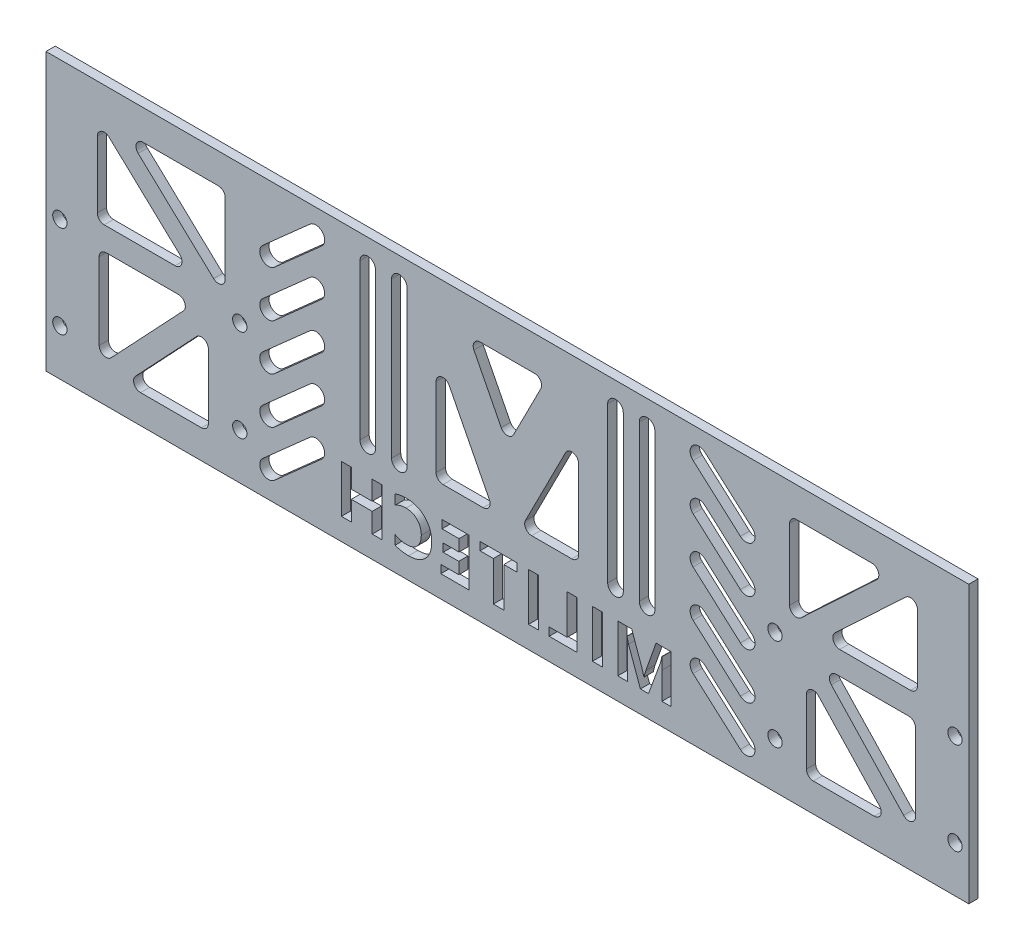
SolidWorks part; units mm, degrees
material "Thornel Mat VMA"
ref_plane "前视基准面" through (0, 0, 0) normal (0, 0, 1) x (1, 0, 0)
ref_plane "上视基准面" through (0, 0, 0) normal (0, 1, 0) x (1, 0, 0)
ref_plane "右视基准面" through (0, 0, 0) normal (1, 0, 0) x (0, 0, -1)
sketch "草图1" plane through (0, 0, 0) normal (0, 0, 1) x (1, 0, 0)
  line L1 (69.1181, 5.8229) -> (69.1181, -30.1771)
  line L2 (69.1181, -30.1771) -> (22.1181, -30.1771)
  line L6 (-83.8819, -30.1771) -> (-130.8819, -30.1771)
  line L7 (-130.8819, -30.1771) -> (-130.8819, 5.8229)
  line L9 (-83.8819, -30.1771) -> (22.1181, -30.1771)
  line L10 (-130.8819, 29.8229) -> (69.1181, 29.8229)
  line L11 (69.1181, 29.8229) -> (69.1181, 5.8229)
  line L12 (-130.8819, 5.8229) -> (-130.8819, 29.8229)
  line L13 (-30.8819, 70.3505) -> (-30.8819, -56.6176) construction
  line L14 (-24.9697, 22.3307) -> (-36.7942, 22.3307)
  line L15 (-38.1307, 20.1497) -> (-32.2185, 8.5463)
  line L21 (-46.3345, 10.1512) -> (-46.3345, -6.9368)
  line L22 (-44.8345, -8.4368) -> (-36.1277, -8.4368)
  line L23 (-34.7912, -6.2558) -> (-43.4979, 10.8322)
  line L25 (-23.6332, 20.1497) -> (-29.5454, 8.5463)
  line L26 (-16.9294, -8.4368) -> (-25.6362, -8.4368)
  line L27 (-15.4294, 10.1512) -> (-15.4294, -6.9368)
  line L28 (-26.9727, -6.2558) -> (-18.2659, 10.8322)
  line L30 (-54.3098, 24.566) -> (-54.3098, -9.0735) construction
  line L31 (-52.6215, 24.566) -> (-52.6215, -9.0735)
  line L32 (-55.9982, 24.566) -> (-55.9982, -9.0735)
  line L33 (-61.1571, 24.566) -> (-61.1571, -9.0735) construction
  line L34 (-59.4687, 24.566) -> (-59.4687, -9.0735)
  line L35 (-62.8454, 24.566) -> (-62.8454, -9.0735)
  line L36 (-0.6068, 24.566) -> (-0.6068, -9.0735) construction
  line L37 (-2.2952, 24.566) -> (-2.2952, -9.0735)
  line L38 (1.0815, 24.566) -> (1.0815, -9.0735)
  line L39 (-7.4541, 24.566) -> (-7.4541, -9.0735) construction
  line L40 (-9.1424, 24.566) -> (-9.1424, -9.0735)
  line L41 (-5.7657, 24.566) -> (-5.7657, -9.0735)
  line L69 (-109.8837, 23.2791) -> (-93.5349, 23.2791)
  line L70 (-119.7574, 19.486) -> (-119.7574, 5.0939)
  line L71 (-118.2574, 3.5939) -> (-102.9058, 3.5939)
  line L72 (-92.0349, 21.7791) -> (-92.0349, 6.4521)
  line L74 (-119.7574, 3.5939) -> (-92.0349, 23.2791) construction
  line L76 (-117.8537, -1.4382) -> (-102.1842, -1.4382)
  line L77 (-119.3537, -2.9382) -> (-119.3537, -19.587)
  line L78 (-110.4007, -23.9653) -> (-97.1915, -23.9653)
  line L79 (-95.6915, -8.4305) -> (-95.6915, -22.4653)
  line L80 (-119.3537, -1.4382) -> (-95.6915, -23.9653) construction
  line L81 (49.7291, -21.4373) -> (36.5199, -7.4024)
  line L82 (-117.2315, 20.5803) -> (-101.8799, 6.1882)
  line L83 (-110.9096, 20.6848) -> (-94.5608, 5.3578)
  line L84 (-101.0919, -3.9662) -> (-116.7614, -20.615)
  line L85 (-111.493, -21.4373) -> (-98.2838, -7.4024)
  line L86 (33.9276, -8.4305) -> (33.9276, -22.4653)
  line L87 (48.6368, -23.9653) -> (35.4276, -23.9653)
  line L88 (57.5899, -2.9382) -> (57.5899, -19.587)
  line L89 (39.3281, -3.9662) -> (54.9976, -20.615)
  line L90 (56.0899, -1.4382) -> (40.4204, -1.4382)
  line L91 (49.1457, 20.6848) -> (32.7969, 5.3578)
  line L92 (30.271, 21.7791) -> (30.271, 6.4521)
  line L93 (48.1198, 23.2791) -> (31.771, 23.2791)
  line L94 (55.4676, 20.5803) -> (40.116, 6.1882)
  line L95 (56.4935, 3.5939) -> (41.1419, 3.5939)
  line L96 (57.9935, 19.486) -> (57.9935, 5.0939)
  line L97 (-72.3936, 24.5989) -> (-82.6502, 15.4916) construction
  line L100 (-71.1291, 23.1748) -> (-81.3858, 14.0675)
  line L101 (-73.6581, 26.0229) -> (-83.9147, 16.9157)
  line L102 (-72.3936, 14.5989) -> (-82.6502, 5.4916) construction
  line L103 (-71.1291, 13.1748) -> (-81.3858, 4.0675)
  line L104 (-73.6581, 16.0229) -> (-83.9147, 6.9157)
  line L105 (-72.3936, 4.5989) -> (-82.6502, -4.5084) construction
  line L106 (-71.1291, 3.1748) -> (-81.3858, -5.9325)
  line L107 (-73.6581, 6.0229) -> (-83.9147, -3.0843)
  line L108 (-72.3936, -5.4011) -> (-82.6502, -14.5084) construction
  line L109 (-71.1291, -6.8252) -> (-81.3858, -15.9325)
  line L110 (-73.6581, -3.9771) -> (-83.9147, -13.0843)
  line L111 (-72.3936, -15.4011) -> (-82.6502, -24.5084) construction
  line L112 (-71.1291, -16.8252) -> (-81.3858, -25.9325)
  line L113 (-73.6581, -13.9771) -> (-83.9147, -23.0843)
  line L114 (10.6297, -15.4011) -> (20.8864, -24.5084) construction
  line L115 (9.3652, -16.8252) -> (19.6219, -25.9325)
  line L116 (11.8942, -13.9771) -> (22.1508, -23.0843)
  line L117 (10.6297, -5.4011) -> (20.8864, -14.5084) construction
  line L118 (9.3652, -6.8252) -> (19.6219, -15.9325)
  line L119 (11.8942, -3.9771) -> (22.1508, -13.0843)
  line L120 (10.6297, 4.5989) -> (20.8864, -4.5084) construction
  line L121 (9.3652, 3.1748) -> (19.6219, -5.9325)
  line L122 (11.8942, 6.0229) -> (22.1508, -3.0843)
  line L123 (10.6297, 14.5989) -> (20.8864, 5.4916) construction
  line L124 (9.3652, 13.1748) -> (19.6219, 4.0675)
  line L125 (11.8942, 16.0229) -> (22.1508, 6.9157)
  line L126 (10.6297, 24.5989) -> (20.8864, 15.4916) construction
  line L127 (9.3652, 23.1748) -> (19.6219, 14.0675)
  line L128 (11.8942, 26.0229) -> (22.1508, 16.9157)
  circle A0 centre (-127.8819, -0.1771) radius 1.55
  circle A1 centre (-127.8819, -20.1771) radius 1.55
  circle A2 centre (-88.8819, -0.1771) radius 1.55
  circle A3 centre (-88.8819, -20.1771) radius 1.55
  circle A4 centre (27.1181, -0.1771) radius 1.55
  circle A5 centre (27.1181, -20.1771) radius 1.55
  circle A6 centre (66.1181, -0.1771) radius 1.55
  circle A7 centre (66.1181, -20.1771) radius 1.55
  arc A8 (-46.3345, 10.1512) -> (-43.4979, 10.8322) centre (-44.8345, 10.1512) cw
  arc A9 (-38.1307, 20.1497) -> (-36.7942, 22.3307) centre (-36.7942, 20.8307) cw
  arc A10 (-46.3345, -6.9368) -> (-44.8345, -8.4368) centre (-44.8345, -6.9368) ccw
  arc A11 (-34.7912, -6.2558) -> (-36.1277, -8.4368) centre (-36.1277, -6.9368) cw
  arc A12 (-23.6332, 20.1497) -> (-24.9697, 22.3307) centre (-24.9697, 20.8307) ccw
  arc A13 (-15.4294, -6.9368) -> (-16.9294, -8.4368) centre (-16.9294, -6.9368) cw
  arc A14 (-15.4294, 10.1512) -> (-18.2659, 10.8322) centre (-16.9294, 10.1512) ccw
  arc A15 (-26.9727, -6.2558) -> (-25.6362, -8.4368) centre (-25.6362, -6.9368) ccw
  arc A16 (-32.2185, 8.5463) -> (-29.5454, 8.5463) centre (-30.8819, 9.2273) ccw
  arc A17 (-52.6215, 24.566) -> (-55.9982, 24.566) centre (-54.3098, 24.566) ccw
  arc A18 (-55.9982, -9.0735) -> (-52.6215, -9.0735) centre (-54.3098, -9.0735) ccw
  arc A19 (-59.4687, 24.566) -> (-62.8454, 24.566) centre (-61.1571, 24.566) ccw
  arc A20 (-62.8454, -9.0735) -> (-59.4687, -9.0735) centre (-61.1571, -9.0735) ccw
  arc A21 (-2.2952, 24.566) -> (1.0815, 24.566) centre (-0.6068, 24.566) cw
  arc A22 (1.0815, -9.0735) -> (-2.2952, -9.0735) centre (-0.6068, -9.0735) cw
  arc A23 (-9.1424, 24.566) -> (-5.7657, 24.566) centre (-7.4541, 24.566) cw
  arc A24 (-5.7657, -9.0735) -> (-9.1424, -9.0735) centre (-7.4541, -9.0735) cw
  arc A25 (-111.493, -21.4373) -> (-110.4007, -23.9653) centre (-110.4007, -22.4653) ccw
  arc A26 (-97.1915, -23.9653) -> (-95.6915, -22.4653) centre (-97.1915, -22.4653) ccw
  arc A27 (-95.6915, -8.4305) -> (-98.2838, -7.4024) centre (-97.1915, -8.4305) ccw
  arc A28 (-102.1842, -1.4382) -> (-101.0919, -3.9662) centre (-102.1842, -2.9382) cw
  arc A29 (-116.7614, -20.615) -> (-119.3537, -19.587) centre (-117.8537, -19.587) cw
  arc A30 (-119.3537, -2.9382) -> (-117.8537, -1.4382) centre (-117.8537, -2.9382) cw
  arc A31 (-101.8799, 6.1882) -> (-102.9058, 3.5939) centre (-102.9058, 5.0939) cw
  arc A32 (-118.2574, 3.5939) -> (-119.7574, 5.0939) centre (-118.2574, 5.0939) cw
  arc A33 (-119.7574, 19.486) -> (-117.2315, 20.5803) centre (-118.2574, 19.486) cw
  arc A34 (-93.5349, 23.2791) -> (-92.0349, 21.7791) centre (-93.5349, 21.7791) cw
  arc A35 (-92.0349, 6.4521) -> (-94.5608, 5.3578) centre (-93.5349, 6.4521) cw
  arc A36 (-110.9096, 20.6848) -> (-109.8837, 23.2791) centre (-109.8837, 21.7791) cw
  arc A37 (33.9276, -8.4305) -> (36.5199, -7.4024) centre (35.4276, -8.4305) cw
  arc A38 (49.7291, -21.4373) -> (48.6368, -23.9653) centre (48.6368, -22.4653) cw
  arc A39 (35.4276, -23.9653) -> (33.9276, -22.4653) centre (35.4276, -22.4653) cw
  arc A40 (54.9976, -20.615) -> (57.5899, -19.587) centre (56.0899, -19.587) ccw
  arc A41 (40.4204, -1.4382) -> (39.3281, -3.9662) centre (40.4204, -2.9382) ccw
  arc A42 (57.5899, -2.9382) -> (56.0899, -1.4382) centre (56.0899, -2.9382) ccw
  arc A43 (30.271, 6.4521) -> (32.7969, 5.3578) centre (31.771, 6.4521) ccw
  arc A44 (31.771, 23.2791) -> (30.271, 21.7791) centre (31.771, 21.7791) ccw
  arc A45 (49.1457, 20.6848) -> (48.1198, 23.2791) centre (48.1198, 21.7791) ccw
  arc A46 (40.116, 6.1882) -> (41.1419, 3.5939) centre (41.1419, 5.0939) ccw
  arc A47 (56.4935, 3.5939) -> (57.9935, 5.0939) centre (56.4935, 5.0939) ccw
  arc A48 (57.9935, 19.486) -> (55.4676, 20.5803) centre (56.4935, 19.486) ccw
  arc A51 (-71.1291, 23.1748) -> (-73.6581, 26.0229) centre (-72.3936, 24.5989) ccw
  arc A52 (-83.9147, 16.9157) -> (-81.3858, 14.0675) centre (-82.6502, 15.4916) ccw
  arc A53 (-71.1291, 13.1748) -> (-73.6581, 16.0229) centre (-72.3936, 14.5989) ccw
  arc A54 (-83.9147, 6.9157) -> (-81.3858, 4.0675) centre (-82.6502, 5.4916) ccw
  arc A55 (-71.1291, 3.1748) -> (-73.6581, 6.0229) centre (-72.3936, 4.5989) ccw
  arc A56 (-83.9147, -3.0843) -> (-81.3858, -5.9325) centre (-82.6502, -4.5084) ccw
  arc A57 (-71.1291, -6.8252) -> (-73.6581, -3.9771) centre (-72.3936, -5.4011) ccw
  arc A58 (-83.9147, -13.0843) -> (-81.3858, -15.9325) centre (-82.6502, -14.5084) ccw
  arc A59 (-71.1291, -16.8252) -> (-73.6581, -13.9771) centre (-72.3936, -15.4011) ccw
  arc A60 (-83.9147, -23.0843) -> (-81.3858, -25.9325) centre (-82.6502, -24.5084) ccw
  arc A61 (9.3652, -16.8252) -> (11.8942, -13.9771) centre (10.6297, -15.4011) cw
  arc A62 (22.1508, -23.0843) -> (19.6219, -25.9325) centre (20.8864, -24.5084) cw
  arc A63 (9.3652, -6.8252) -> (11.8942, -3.9771) centre (10.6297, -5.4011) cw
  arc A64 (22.1508, -13.0843) -> (19.6219, -15.9325) centre (20.8864, -14.5084) cw
  arc A65 (9.3652, 3.1748) -> (11.8942, 6.0229) centre (10.6297, 4.5989) cw
  arc A66 (22.1508, -3.0843) -> (19.6219, -5.9325) centre (20.8864, -4.5084) cw
  arc A67 (9.3652, 13.1748) -> (11.8942, 16.0229) centre (10.6297, 14.5989) cw
  arc A68 (22.1508, 6.9157) -> (19.6219, 4.0675) centre (20.8864, 5.4916) cw
  arc A69 (9.3652, 23.1748) -> (11.8942, 26.0229) centre (10.6297, 24.5989) cw
  arc A70 (22.1508, 16.9157) -> (19.6219, 14.0675) centre (20.8864, 15.4916) cw
  text T0 "MILITECH" font "微软雅黑" height in points 36
  point P44 (-30.8819, 22.3307)
  point P55 (-30.8819, 5.9232)
  point P58 (-54.3098, 7.7463)
  point P63 (-61.1571, 7.7463)
  point P72 (-0.6068, 7.7463)
  point P79 (-7.4541, 7.7463)
  point P84 (-106.2813, 13.163)
  point P89 (-106.8773, -13.3161)
  point P164 (-77.5219, 20.0452)
  point P172 (-77.5219, 10.0452)
  point P179 (-77.5219, 0.0452)
  point P186 (-77.5219, -9.9548)
  point P193 (-77.5219, -19.9548)
  point P200 (15.758, -19.9548)
  point P207 (15.758, -9.9548)
  point P214 (15.758, 0.0452)
  point P221 (15.758, 10.0452)
  point P228 (15.758, 20.0452)
  dimension "D7" = 3
  dimension "D3" = 24
  dimension "D10" = 30
  dimension "D15" = 30
  dimension "D16" = 1.5
  dimension "D23" = 5
  dimension "D19" = 1.5
  dimension "D21" = 1.5
  dimension "D4" = 1.5
  dimension "D1" = 47
  dimension "D2" = 47
  dimension "D5" = 5
  dimension "D6" = 5
  dimension "D8" = 3
  dimension "D9" = 100
  dimension "D11" = 30
  dimension "D12" = 20
  dimension "D13" = 30
  dimension "D14" = 20
  dimension "D17" = 3
  dimension "D18" = 3
  dimension "D20" = 20
  dimension "D22" = 20
extrude "凸台-拉伸1" add sketch "草图1" along normal blind 2
